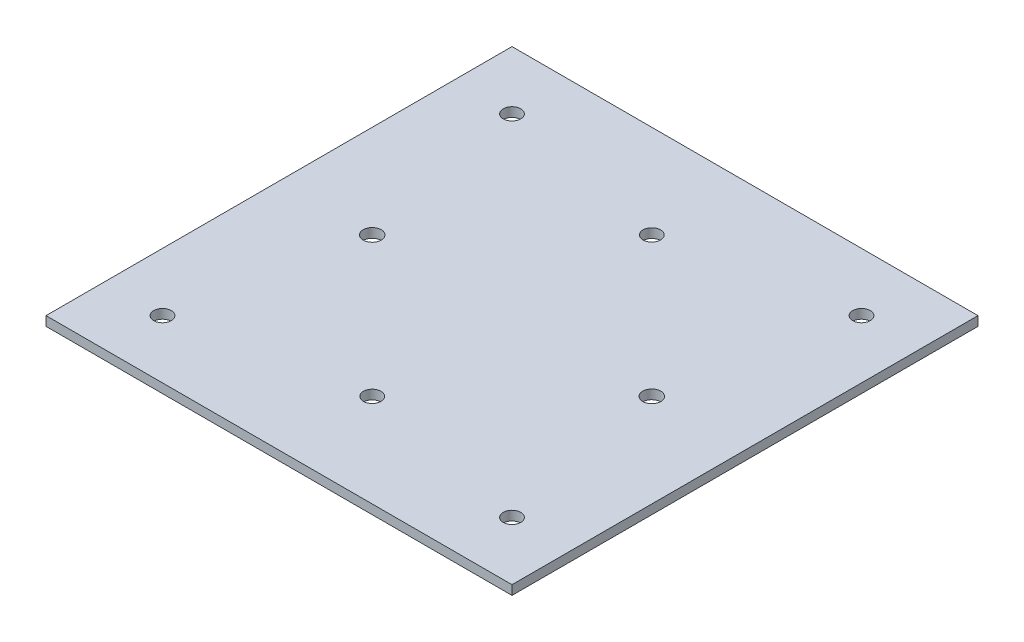
SolidWorks part; units mm, degrees
material "A-Glass Fiber"
ref_plane "Front Plane" through (0, 0, 0) normal (0, 0, 1) x (1, 0, 0)
ref_plane "Top Plane" through (0, 0, 0) normal (0, 1, 0) x (1, 0, 0)
ref_plane "Right Plane" through (0, 0, 0) normal (1, 0, 0) x (0, 0, -1)
sketch "Sketch2" plane through (0, 0, 0) normal (0, 1, 0) x (1, 0, 0)
  line L1 (0, 0) -> (96, 0)
  line L2 (0, 0) -> (0, 96)
  line L3 (0, 96) -> (96, 96)
  line L4 (96, 0) -> (96, 96)
  dimension "D1" = 96
  dimension "D2" = 96
extrude "Boss-Extrude1" add sketch "Sketch2" along normal blind 1.6
sketch "Sketch3" plane through (0, 1.6, 0) normal (0, 1, 0) x (1, 0, 0)
  line L0 (0, 96) -> (0, 0) construction
  line L1 (0, 48) -> (96, 48) construction
  line L2 (96, 0) -> (96, 96) construction
  line L3 (48, 0) -> (48, 96) construction
  line L4 (0, 0) -> (96, 0) construction
  line L5 (96, 96) -> (0, 96) construction
  circle A0 centre (24, 48) radius 1.55
  circle A1 centre (72, 48) radius 1.55
  circle A2 centre (48, 72) radius 1.505
  circle A3 centre (48, 24) radius 1.505
  circle A4 centre (18, 78) radius 1.505
  circle A5 centre (78, 78) radius 1.505
  circle A6 centre (78, 18) radius 1.505
  circle A7 centre (18, 18) radius 1.505
  dimension "D2" = 3.1
  dimension "D3" = 3.01
  dimension "D5" = 3.01
  dimension "D1" = 24
  dimension "D4" = 24
  dimension "D6" = 18
  dimension "D7" = 18
extrude "Cut-Extrude1" cut sketch "Sketch3" against normal through all
sketch "Sketch4" plane through (0, 1.6, 0) normal (0, 1, 0) x (1, 0, 0)
  line L0 (96, 96) -> (0, 96) construction
  line L1 (8, 88) -> (88, 88)
  line L2 (8, 88) -> (8, 8)
  line L3 (8, 8) -> (88, 8)
  line L4 (88, 88) -> (88, 8)
  line L7 (0, 96) -> (0, 0) construction
  line L8 (48, 96) -> (48, 0) construction
  line L10 (0, 48) -> (96, 48) construction
  line L11 (96, 0) -> (96, 96) construction
  line L12 (0, 0) -> (96, 0) construction
  point P4 (47.8833, 48.958)
  dimension "D1" = 80
extrude "Cut-Extrude2" cut sketch "Sketch4" against normal blind 10 flip side to cut
